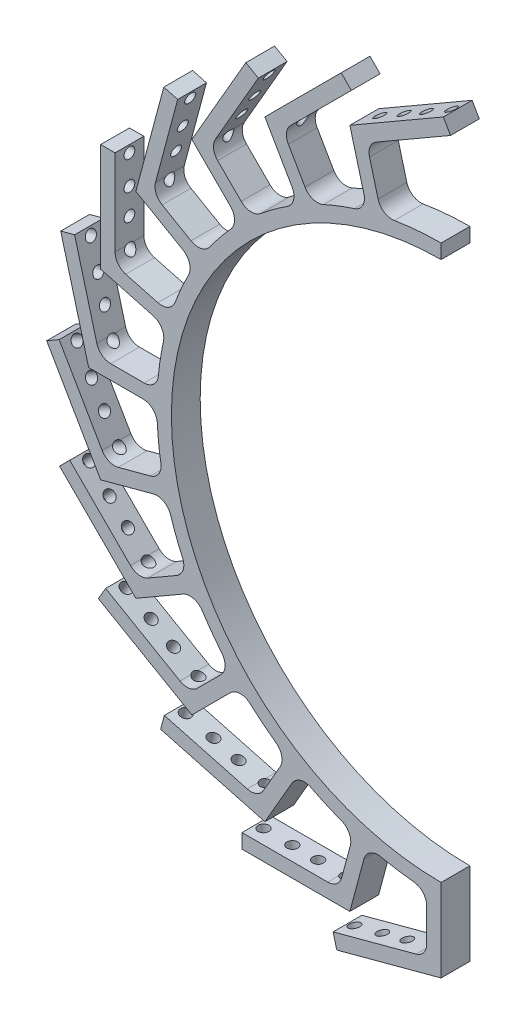
SolidWorks part; units mm, degrees
material "Polyetheretherketone (PEEK)"
ref_plane "Front Plane" through (0, 0, 0) normal (0, 0, 1) x (1, 0, 0)
ref_plane "Top Plane" through (0, 0, 0) normal (0, 1, 0) x (1, 0, 0)
ref_plane "Right Plane" through (0, 0, 0) normal (1, 0, 0) x (0, 0, -1)
sketch "Sketch1" plane through (0, 0, 0) normal (0, 0, 1) x (1, 0, 0)
  line L0 (0, -125.349) -> (0, -118.999)
  line L1 (0, 118.999) -> (0, 0) construction
  line L2 (0, 118.999) -> (0, 125.349)
  arc A0 (0, 125.349) -> (0, -125.349) centre (0, 0) ccw
  arc A1 (0, 118.999) -> (0, -118.999) centre (0, 0) ccw
  dimension "D1" = 118.999
  dimension "D2" = 6.35
extrude "Boss-Extrude1" add sketch "Sketch1" along normal blind 12.7
sketch "Sketch2" plane through (0, 0, 12.7) normal (0, 0, 1) x (1, 0, 0)
  line L0 (0, -125.349) -> (0, -155.5115)
  line L1 (0, -155.5115) -> (-46.0022, -167.8378)
  line L2 (-46.0022, -167.8378) -> (-47.6457, -161.7041)
  line L3 (-47.6457, -161.7041) -> (-6.35, -150.639)
  line L4 (-6.35, -150.639) -> (-6.35, -125.1881)
  arc A1 (-6.35, -125.1881) -> (0, -125.349) centre (0, 0) ccw
  arc A2 (0, 125.349) -> (0, -125.349) centre (0, 0) ccw construction
  dimension "D1" = 6.35
  dimension "D2" = 6.35
  dimension "D3" = 47.625
  dimension "D4" = 105
  dimension "D5" = 30.1625
extrude "Boss-Extrude2" add sketch "Sketch2" against normal up to surface (12.7 mm away) up to face at (-61.087, 0, 0)
fillet "Fillet1" radius 6.35 2 edges at (-6.35, -125.1881, 6.35) (-6.35, -150.639, 6.35)
pattern_circular "CirPattern1" count 12 every 15 about axis through (0, 0, 0) along (0, 0, 1) of "Boss-Extrude2"
fillet "Fillet2" radius 6.35 33 edges at (-45.1219, -143.8626, 6.35) (-38.5347, -119.2789, 6.35) (-32.4427, -121.0778, 6.35) (-32.8546, 147.1496, 6.35) (-69.8202, 133.6322, 6.35) (-102.0277, 111.008, 6.35) (-127.2822, 80.8187, 6.35) (-121.0778, 32.4427, 6.35) (-108.5554, 62.6745, 6.35) (-88.6351, 88.6351, 6.35) (-62.6745, 108.5554, 6.35) (-32.4427, 121.0778, 6.35) (-26.2674, 122.5659, 6.35) (-57.0948, 111.591, 6.35) (-84.0312, 93.0115, 6.35) (-105.241, 68.0933, 6.35) (-119.2789, 38.5347, 6.35) (-143.8626, 45.1219, 6.35) (-125.1881, 6.35, 6.35) (-150.639, 6.35, 6.35) (-125.349, 0, 6.35) (-121.0778, -32.4427, 6.35) (-122.5659, -26.2674, 6.35) (-147.1496, -32.8546, 6.35) (-133.6322, -69.8202, 6.35) (-111.591, -57.0948, 6.35) (-108.5554, -62.6745, 6.35) (-88.6351, -88.6351, 6.35) (-93.0115, -84.0312, 6.35) (-111.008, -102.0277, 6.35) (-80.8187, -127.2822, 6.35) (-68.0933, -105.241, 6.35) (-62.6745, -108.5554, 6.35)
sketch "Sketch3" plane through (38.8779, -145.0942, 0) normal (0.2588, -0.9659, 0) x (0.9659, 0.2588, 0)
  line L0 (-40.2493, 6.35) -> (-87.8743, 6.35) construction
  line L1 (-40.2493, 0) -> (-40.2493, 12.7) construction
  line L2 (-87.8743, 0) -> (-87.8743, 12.7) construction
  circle A0 centre (-48.1868, 6.35) radius 2.3812
  circle A1 centre (-84.6993, 6.35) radius 2.3813
  circle A2 centre (-60.5693, 6.35) radius 2.3812
  circle A3 centre (-71.9993, 6.35) radius 2.3813
  dimension "D1" = 4.7625
  dimension "D2" = 3.175
  dimension "D3" = 7.9375
  dimension "D4" = 20.32
  dimension "D5" = 31.75
extrude "Cut-Extrude1" cut sketch "Sketch3" against normal blind 12.7
pattern_circular "CirPattern8" count 12 every 15 about axis through (0, 0, 12.7) along (0, 0, -1) of "Cut-Extrude1"
